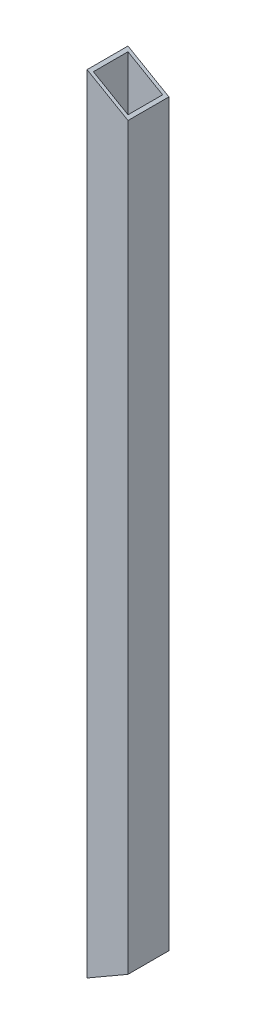
SolidWorks part; units mm, degrees
ref_plane "Front Plane" through (0, 0, 0) normal (0, 0, 1) x (1, 0, 0)
ref_plane "Top Plane" through (0, 0, 0) normal (0, 1, 0) x (1, 0, 0)
ref_plane "Right Plane" through (0, 0, 0) normal (1, 0, 0) x (0, 0, -1)
sketch "Sketch4" plane through (0, 0, 0) normal (0, 1, 0) x (1, 0, 0)
  line L0 (-6.1172, 6.4694) -> (6.8828, 6.4694)
  line L1 (-5.1172, 5.4694) -> (5.8828, 5.4694)
  line L2 (-5.1172, 5.4694) -> (-5.1172, -5.5306)
  line L3 (-5.1172, -5.5306) -> (5.8828, -5.5306)
  line L4 (5.8828, 5.4694) -> (5.8828, -5.5306)
  line L5 (6.8828, 6.4694) -> (6.8828, -6.5306)
  line L6 (-6.1172, -6.5306) -> (6.8828, -6.5306)
  line L7 (-6.1172, 6.4694) -> (-6.1172, -6.5306)
  dimension "D1" = 11
  dimension "D2" = 11
  dimension "D3" = 1
extrude "Boss-Extrude1" add sketch "Sketch4" along normal blind 250
sketch "Sketch5" plane through (0, 0, 6.5306) normal (0, 0, 1) x (1, 0, 0)
  line L0 (-6.1172, 250) -> (6.8828, 242.4944)
  line L1 (6.8828, 250) -> (6.8828, 0) construction
  line L2 (-6.1172, 0) -> (6.8828, 7.5056)
  line L3 (6.8828, 242.4944) -> (6.8828, 250)
  line L4 (6.8828, 250) -> (-6.1172, 250)
  line M1 (-6.1172, 0) -> (6.8828, 0)
  line M2 (6.8828, 0) -> (6.8828, 250)
  line M3 (6.8828, 250) -> (-6.1172, 250)
extrude "Cut-Extrude1" cut sketch "Sketch5" against normal through all contours L2 M1 M2 | L0 M3 M2
